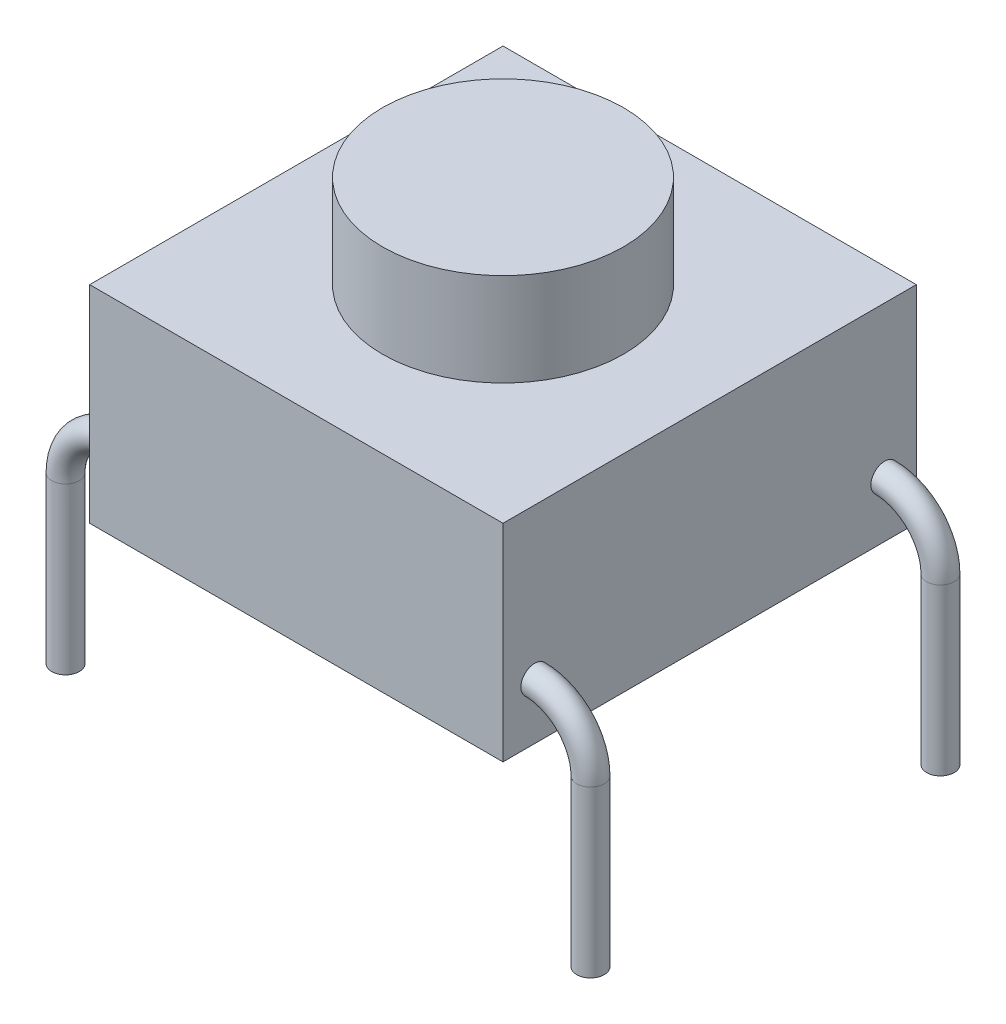
SolidWorks part; units mm, degrees
ref_plane "Front Plane" through (0, 0, 0) normal (0, 0, 1) x (1, 0, 0)
ref_plane "Top Plane" through (0, 0, 0) normal (0, 1, 0) x (1, 0, 0)
ref_plane "Right Plane" through (0, 0, 0) normal (1, 0, 0) x (0, 0, -1)
sketch "Sketch1" plane through (0, 0, 0) normal (0, 1, 0) x (1, 0, 0)
  line L1 (3, -3) -> (-3, -3)
  line L2 (3, -3) -> (3, 3)
  line L3 (3, 3) -> (-3, 3)
  line L4 (-3, -3) -> (-3, 3)
  line L5 (3, -3) -> (-3, 3) construction
  line L6 (3, 3) -> (-3, -3) construction
  point P0 (0, 0)
  dimension "D1" = 6
  dimension "D2" = 6
extrude "Boss-Extrude1" add sketch "Sketch1" along normal blind 3
sketch "Sketch2" plane through (0, 3, 0) normal (0, 1, 0) x (1, 0, 0)
  circle A0 centre (0, 0) radius 1.75
  dimension "D1" = 3.5
extrude "Boss-Extrude2" add sketch "Sketch2" along normal blind 1.35
sketch "Sketch3" plane through (0, 0, 0) normal (0, -1, 0) x (1, 0, 0)
  line L1 (3.81, -2.54) -> (-3.81, -2.54) construction
  line L2 (3.81, -2.54) -> (3.81, 2.54) construction
  line L3 (3.81, 2.54) -> (-3.81, 2.54) construction
  line L4 (-3.81, -2.54) -> (-3.81, 2.54) construction
  line L5 (3.81, -2.54) -> (-3.81, 2.54) construction
  line L6 (3.81, 2.54) -> (-3.81, -2.54) construction
  circle A0 centre (-3.81, 2.54) radius 0.2
  circle A1 centre (3.81, 2.54) radius 0.2
  circle A2 centre (3.81, -2.54) radius 0.2
  circle A3 centre (-3.81, -2.54) radius 0.2
  point P0 (0, 0)
  dimension "D1" = 0.4
  dimension "D2" = 7.62
  dimension "D3" = 5.08
extrude "Boss-Extrude3" add sketch "Sketch3" along normal blind 2.4 separate body
ref_plane "Plane1" through (0, 0, 2.54) normal (0, 0, 1) x (1, 0, 0)
sketch "Sketch4" plane through (0, 0, 2.54) normal (0, 0, 1) x (1, 0, 0)
  line L0 (-3.61, 0) -> (-4.01, 0) construction
  line L1 (-3, 3) -> (-3, 0) construction
  arc A0 (-3.81, 0) -> (-3, 0.81) centre (-3, 0) cw
sweep "Sweep1" add path "Sketch4" circular profile diameter 0.4 parameters "D3"=0.4
mirror "Mirror1" about plane through (0, 0, 0) normal (1, 0, 0) of "Sweep1" second plane through (0, 0, 0) second plane normal (0, 0, 1)
equation "\"D2@Sketch3\"=2.54*3"
